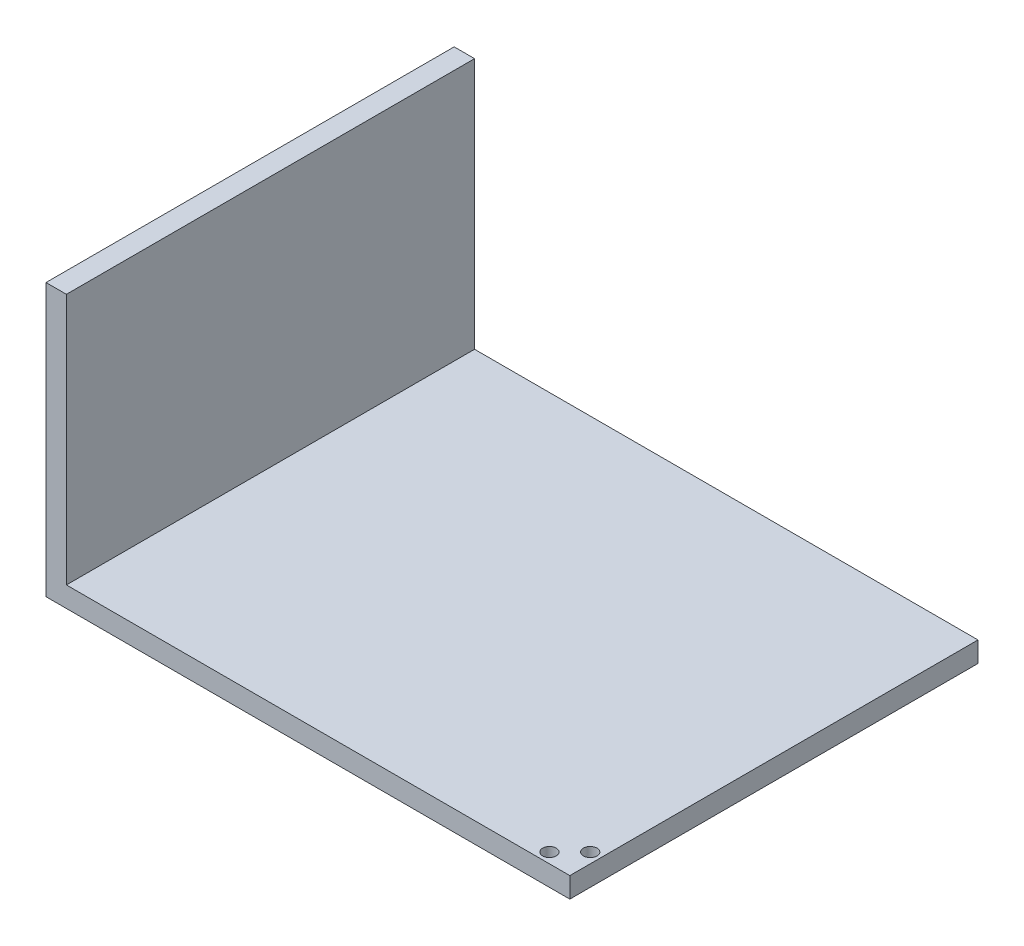
SolidWorks part; units mm, degrees
ref_plane "Front Plane" through (0, 0, 0) normal (0, 0, 1) x (1, 0, 0)
ref_plane "Top Plane" through (0, 0, 0) normal (0, 1, 0) x (1, 0, 0)
ref_plane "Right Plane" through (0, 0, 0) normal (1, 0, 0) x (0, 0, -1)
sketch "Sketch1" plane through (0, 0, 0) normal (0, 1, 0) x (1, 0, 0)
  line L0 (0, 0) -> (200, 0)
  line L1 (200, 0) -> (200, 150)
  line L2 (200, 150) -> (0, 150)
  line L3 (0, 150) -> (0, 0)
  line L4 (0, 150) -> (7.5, 150)
  line L5 (7.5, 150) -> (7.5, 0)
extrude "Boss-Extrude1" add sketch "Sketch1" along normal blind 7.5 contours L2 L5 L0 L1
sketch "Sketch2" plane through (0, 7.5, 0) normal (0, 1, 0) x (1, 0, 0)
  line L0 (7.5, 150) -> (15, 150)
  line L1 (200, 150) -> (7.5, 150) construction
  line L2 (15, 150) -> (15, 0)
  line L3 (7.5, 0) -> (200, 0) construction
  line L4 (15, 0) -> (7.5, 0)
  line L5 (7.5, 0) -> (7.5, 150)
extrude "Boss-Extrude2" add sketch "Sketch2" along normal blind 92.5
sketch "Sketch3" plane through (0, 0, 0) normal (0, -1, 0) x (1, 0, 0)
  line L0 (200, 0) -> (192.5, 0)
  line L1 (7.5, 0) -> (200, 0) construction
  line L6 (200, 0) -> (192.5, -7.5)
  line L10 (192.5, -7.5) -> (169.9632, -7.5)
  line L11 (169.9632, -7.5) -> (192.5, -7.5)
  line L12 (192.5, -7.5) -> (192.5, -21.7693)
  circle A1 centre (188.75, -3.75) radius 2.5
  circle A2 centre (196.25, -11.25) radius 2.5
extrude "Cut-Extrude1" cut sketch "Sketch3" against normal blind 92.5 contours A1 | A2
